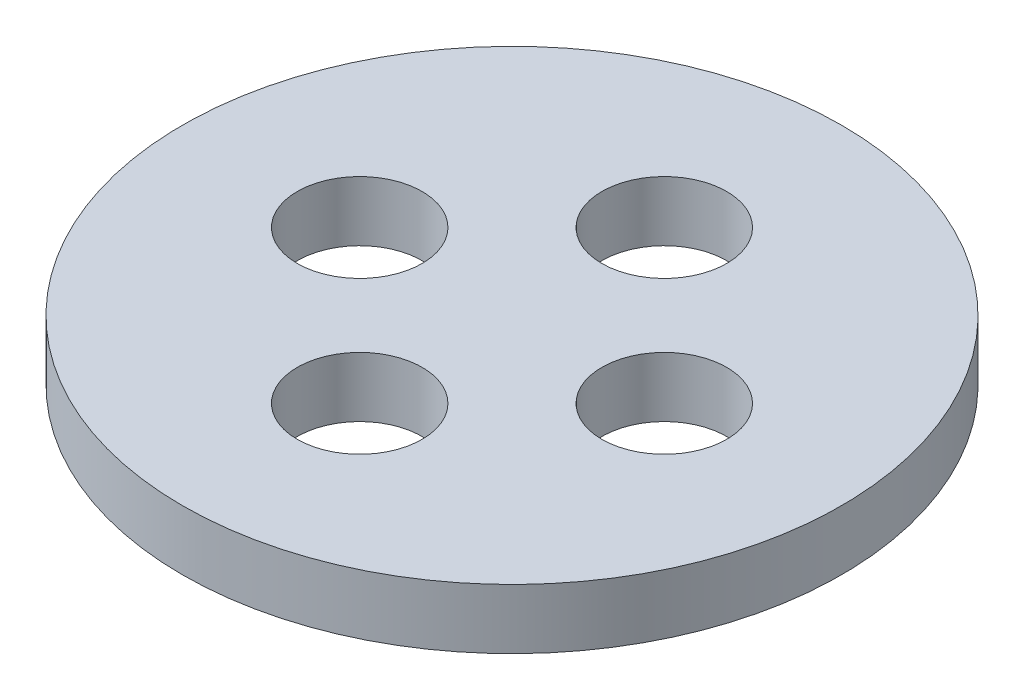
SolidWorks part; units mm, degrees
ref_plane "正面" through (0, 0, 0) normal (0, 0, 1) x (1, 0, 0)
ref_plane "平面" through (0, 0, 0) normal (0, 1, 0) x (1, 0, 0)
ref_plane "右側面" through (0, 0, 0) normal (1, 0, 0) x (0, 0, -1)
sketch "ｽｹｯﾁ1" plane through (0, 0, 0) normal (0, 1, 0) x (1, 0, 0)
  circle A0 centre (0, 0) radius 66
  circle A2 centre (0, 30.5) radius 12.5
  circle A3 centre (30.5, 0) radius 12.5
  circle A5 centre (0, -30.5) radius 12.5
  circle A7 centre (-30.5, 0) radius 12.5
  dimension "D1" = 132
  dimension "D2" = 25
  dimension "D3" = 25
  dimension "D4" = 25
  dimension "D5" = 25
  dimension "D6" = 30.5
  dimension "D7" = 30.5
  dimension "D8" = 30.5
  dimension "D9" = 30.5
extrude "ﾎﾞｽ - 押し出し1" add sketch "ｽｹｯﾁ1" along normal blind 12
